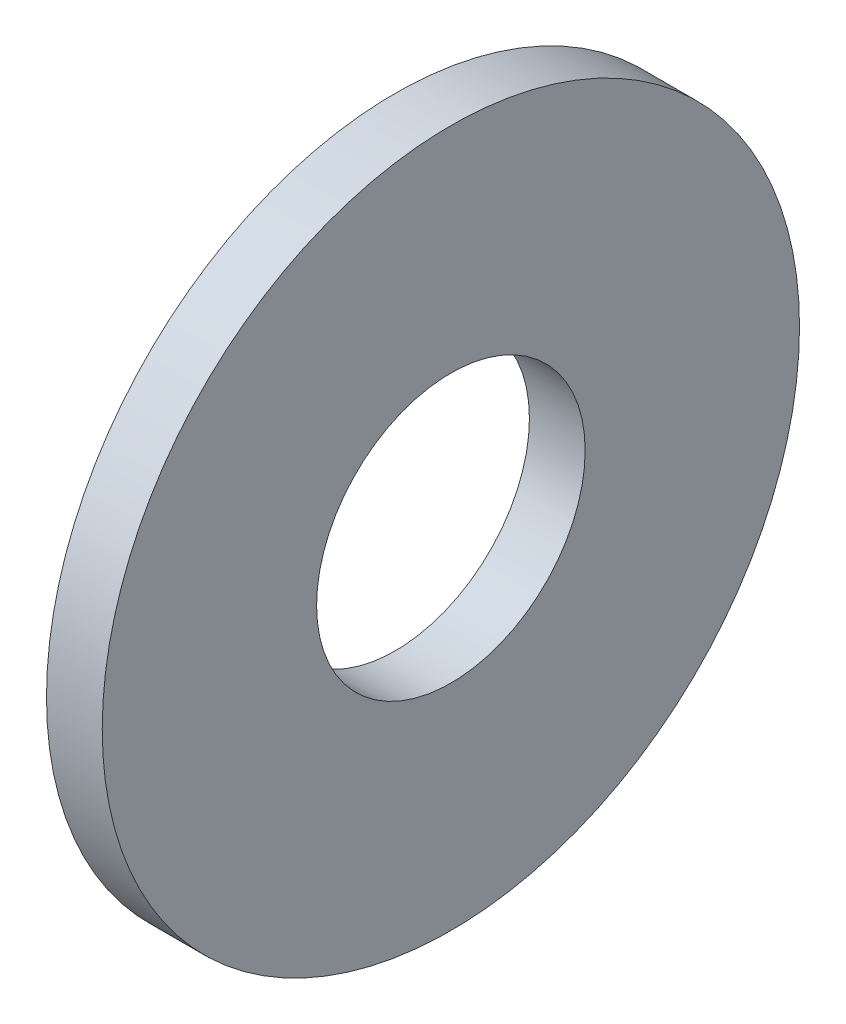
SolidWorks part; units mm, degrees
ref_plane "Front Plane" through (0, 0, 0) normal (0, 0, 1) x (1, 0, 0)
ref_plane "Top Plane" through (0, 0, 0) normal (0, 1, 0) x (1, 0, 0)
ref_plane "Right Plane" through (0, 0, 0) normal (1, 0, 0) x (0, 0, -1)
sketch "Sketch1" plane through (0, 0, 0) normal (1, 0, 0) x (0, 0, -1)
  circle A0 centre (0, 0) radius 8.7376
  circle A1 centre (0, 0) radius 3.3655
  dimension "OD" = 17.4752
  dimension "ID" = 6.731
extrude "Boss-Extrude1" add sketch "Sketch1" along normal blind 1.397
